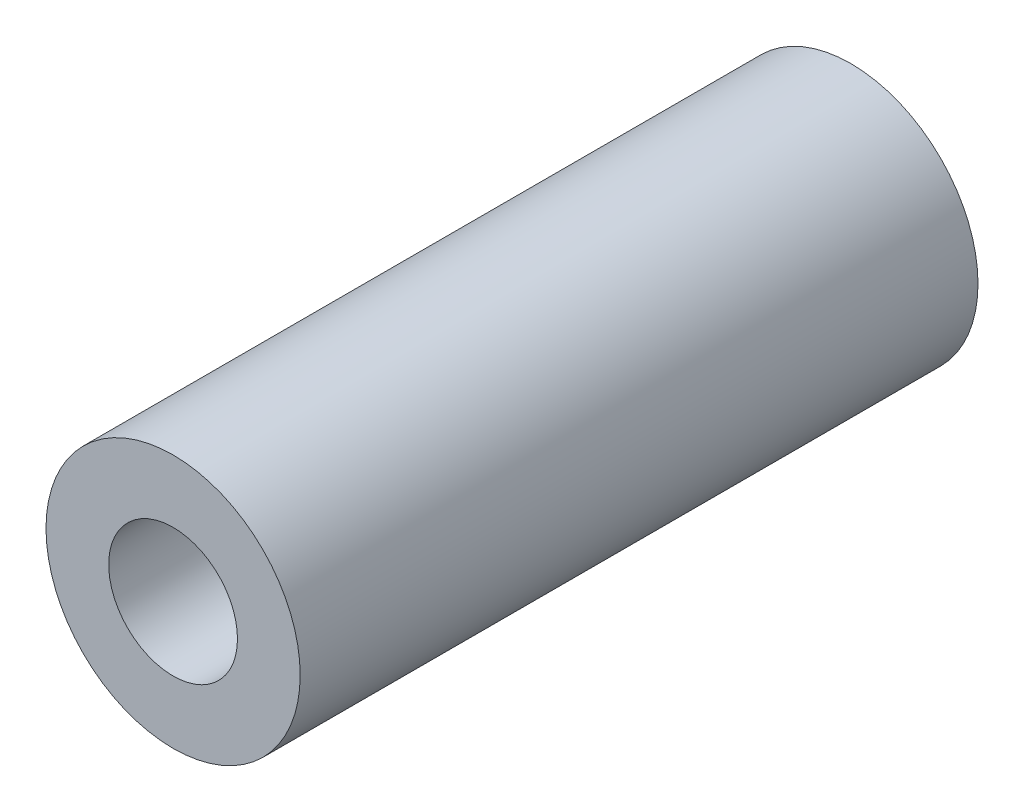
SolidWorks part; units mm, degrees
ref_plane "Ön Düzlem" through (0, 0, 0) normal (0, 0, 1) x (1, 0, 0)
ref_plane "Üst Düzlem" through (0, 0, 0) normal (0, 1, 0) x (1, 0, 0)
ref_plane "Sağ Düzlem" through (0, 0, 0) normal (1, 0, 0) x (0, 0, -1)
sketch "Çizim1" plane through (0, 0, 0) normal (0, 0, 1) x (1, 0, 0)
  circle A0 centre (0, 0) radius 4.826
  circle A1 centre (0, 0) radius 9.525
  dimension "D1" = 19.05
  dimension "D2" = 9.652
extrude "Yükseklik-Ekstrüzyon1" add sketch "Çizim1" along normal blind 50.8
